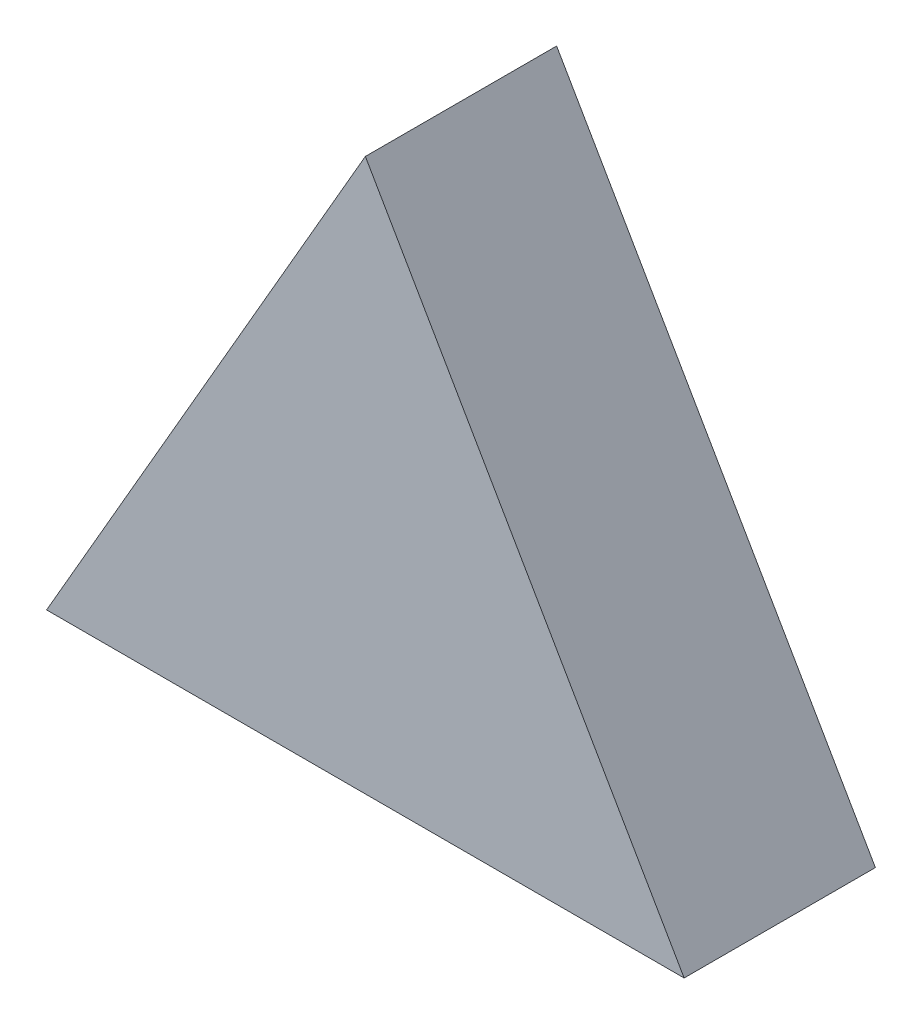
SolidWorks part; units mm, degrees
ref_plane "Front Plane" through (0, 0, 0) normal (0, 0, 1) x (1, 0, 0)
ref_plane "Top Plane" through (0, 0, 0) normal (0, 1, 0) x (1, 0, 0)
ref_plane "Right Plane" through (0, 0, 0) normal (1, 0, 0) x (0, 0, -1)
sketch "Sketch1" plane through (0, 0, 0) normal (0, 0, 1) x (1, 0, 0)
  line L0 (0, 17.3205) -> (10, 0)
  line L1 (10, 0) -> (-10, 0)
  line L2 (-10, 0) -> (0, 17.3205)
  dimension "D1" = 10
  dimension "D2" = 10
  dimension "D3" = 20
  dimension "D4" = 20
extrude "Boss-Extrude1" add sketch "Sketch1" along normal blind 6
